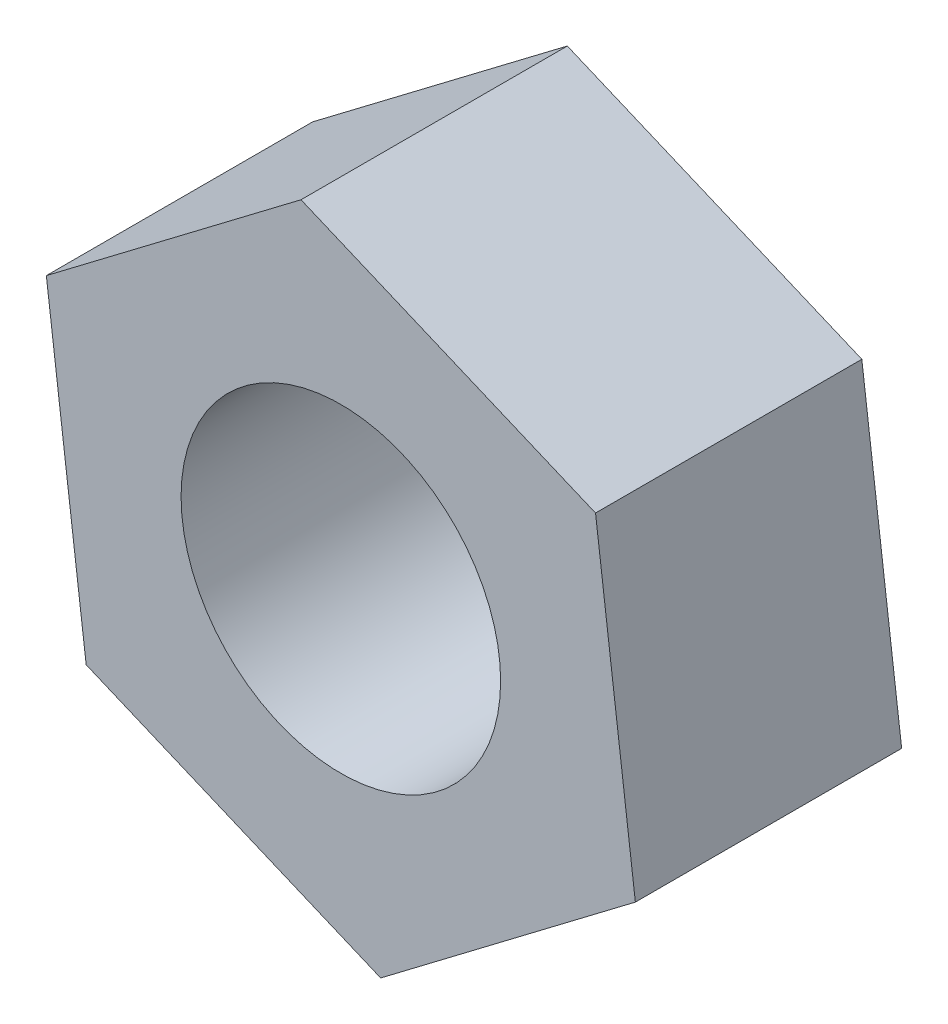
SolidWorks part; units mm, degrees
material "Brass"
ref_plane "Front Plane" through (0, 0, 0) normal (0, 0, 1) x (1, 0, 0)
ref_plane "Top Plane" through (0, 0, 0) normal (0, 1, 0) x (1, 0, 0)
ref_plane "Right Plane" through (0, 0, 0) normal (1, 0, 0) x (0, 0, -1)
sketch "Sketch1" plane through (0, 0, 0) normal (0, 0, 1) x (1, 0, 0)
  line L1 (4.7817, 3.6243) -> (-0.7479, 5.9532)
  line L2 (-0.7479, 5.9532) -> (-5.5296, 2.3289)
  line L3 (-5.5296, 2.3289) -> (-4.7817, -3.6243)
  line L4 (-4.7817, -3.6243) -> (0.7479, -5.9532)
  line L5 (0.7479, -5.9532) -> (5.5296, -2.3289)
  line L6 (5.5296, -2.3289) -> (4.7817, 3.6243)
  circle A0 centre (0, 0) radius 5.1962 construction
  circle A1 centre (0, 0) radius 3
  dimension "D2" = 6
  dimension "D1" = 6
extrude "Boss-Extrude1" add sketch "Sketch1" along normal blind 5
